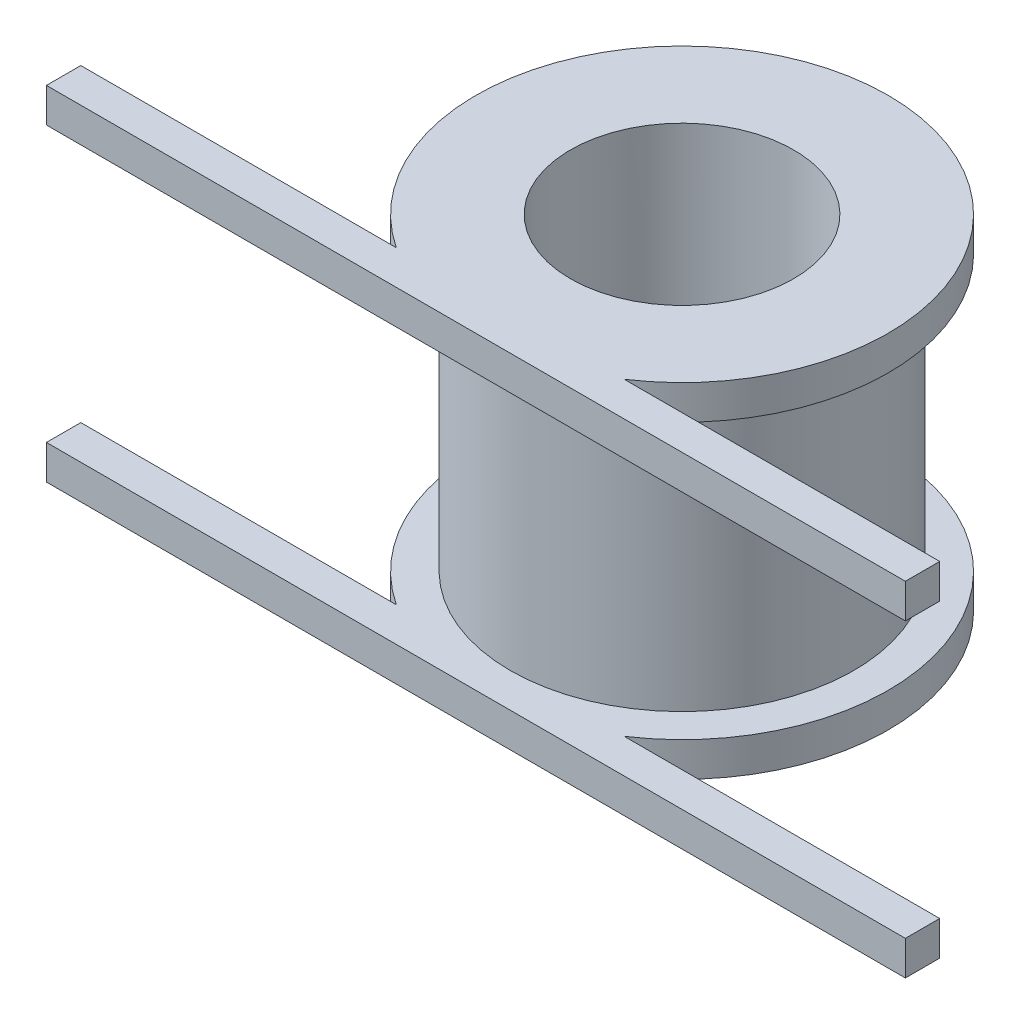
SolidWorks part; units mm, degrees
ref_plane "前视基准面" through (0, 0, 0) normal (0, 0, 1) x (1, 0, 0)
ref_plane "上视基准面" through (0, 0, 0) normal (0, 1, 0) x (1, 0, 0)
ref_plane "右视基准面" through (0, 0, 0) normal (1, 0, 0) x (0, 0, -1)
sketch "草图1" plane through (0, 0, 0) normal (0, 1, 0) x (1, 0, 0)
  line L1 (-25, -10) -> (25, -10)
  line L2 (-25, -10) -> (-25, -12)
  line L3 (-25, -12) -> (25, -12)
  line L4 (25, -10) -> (25, -12)
  circle A0 centre (0, 0) radius 6.5
  circle A1 centre (0, 0) radius 10
extrude "凸台-拉伸1" add sketch "草图1" along normal blind 20 contours A1 A0 | L4 L1 L2 L3
sketch "草图2" plane through (-25, 0, 0) normal (-1, 0, 0) x (0, 0, 1)
  line L0 (12, 20) -> (12, 0) construction
  line L1 (12, 2) -> (10, 2)
  line L2 (12, 2) -> (12, 18)
  line L3 (12, 18) -> (10, 18)
  line L4 (10, 2) -> (10, 18)
  line L5 (10, 20) -> (10, 0) construction
extrude "切除-拉伸2" cut sketch "草图2" against normal blind 50
sketch "草图3" plane through (0, 0, 0) normal (0, 1, 0) x (1, 0, 0)
  circle A0 centre (0, 0) radius 12
extrude "凸台-拉伸2" add sketch "草图3" along normal blind 2
sketch "草图4" plane through (0, 0, 0) normal (0, -1, 0) x (1, 0, 0)
  circle A0 centre (0, 0) radius 6.5
sketch "草图5" plane through (0, 20, 0) normal (0, 1, 0) x (1, 0, 0)
  circle A0 centre (0, 0) radius 12
  circle A1 centre (0, 0) radius 6.5
extrude "凸台-拉伸3" add sketch "草图5" against normal blind 2
extrude "切除-拉伸4" cut sketch "草图4" against normal blind 2
